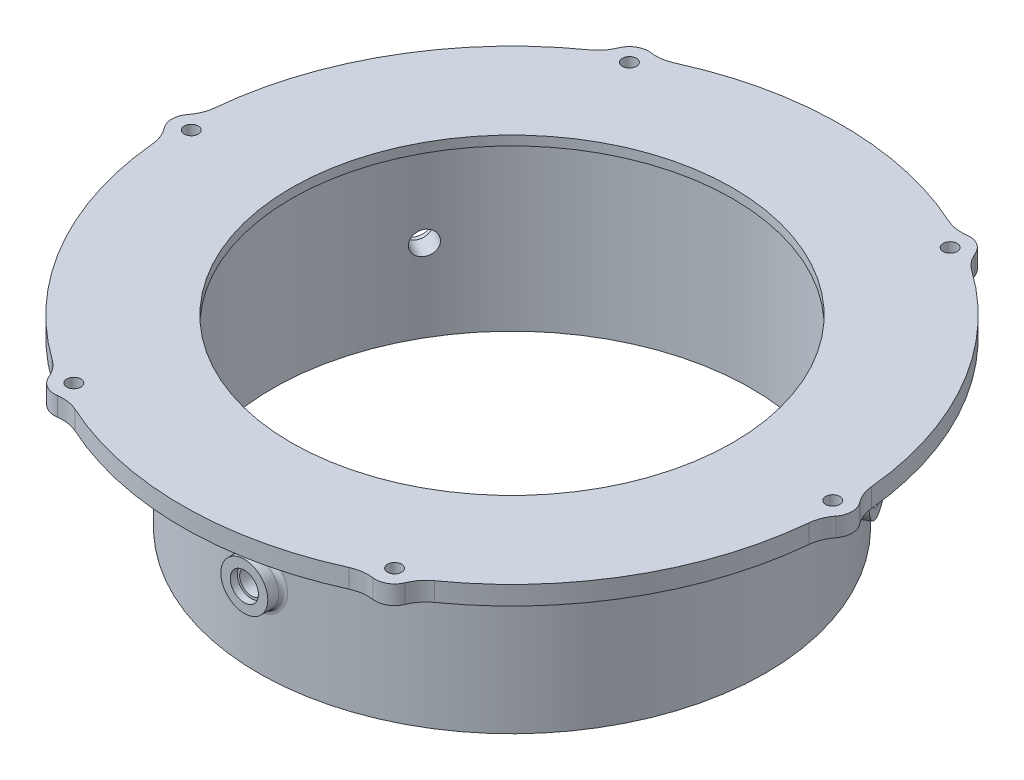
SolidWorks part; units mm, degrees
material "PET"
ref_plane "Front Plane" through (0, 0, 0) normal (0, 0, 1) x (1, 0, 0)
ref_plane "Top Plane" through (0, 0, 0) normal (0, 1, 0) x (1, 0, 0)
ref_plane "Right Plane" through (0, 0, 0) normal (1, 0, 0) x (0, 0, -1)
sketch "Sketch2" plane through (0, 0, 0) normal (0, 0, 1) x (1, 0, 0)
  line L0 (-70.2, -3.2) -> (-47, -3.2)
  line L1 (-47, -3.2) -> (-47, -5.2)
  line L2 (-47, -5.2) -> (-51, -5.2)
  line L3 (-51, -5.2) -> (-51, -42.2)
  line L4 (-51, -42.2) -> (-54, -42.2)
  line L5 (-54, -42.2) -> (-54, -7.2)
  line L6 (-54, -7.2) -> (-70.2, -7.2)
  line L7 (-70.2, -7.2) -> (-70.2, -3.2)
  line L9 (0, 0) -> (0, 30.013) construction
sketch "Sketch3" plane through (0, 0, 0) normal (0, 0, 1) x (1, 0, 0)
  line L8 (-47, -3.2) -> (-70.2, -3.2)
  line L9 (-47, -5.2) -> (-47, -3.2)
  line L10 (-51, -5.2) -> (-47, -5.2)
  line L11 (-51, -42.2) -> (-51, -5.2)
  line L12 (-54, -42.2) -> (-51, -42.2)
  line L13 (-54, -7.2) -> (-54, -42.2)
  line L14 (-70.2, -7.2) -> (-54, -7.2)
  line L15 (-70.2, -3.2) -> (-70.2, -7.2)
  line L16 (-47, -3.2) -> (-70.2, -3.2)
  line L17 (-47, -5.2) -> (-47, -3.2)
  line L18 (-51, -5.2) -> (-47, -5.2)
  line L19 (-51, -42.2) -> (-51, -5.2)
  line L20 (-54, -42.2) -> (-51, -42.2)
  line L21 (-54, -7.2) -> (-54, -42.2)
  line L22 (-70.2, -7.2) -> (-54, -7.2)
  line L23 (-70.2, -3.2) -> (-70.2, -7.2)
  dimension "D1" = 0
revolve "FRA400 100mm" add sketch "Sketch3" angle 360 about L9
sketch "Sketch4" plane through (0, 0, 0) normal (0, 1, 0) x (1, 0, 0)
  circle A0 centre (-68.3, 0) radius 4.1
  circle A1 centre (-68.3, 0) radius 2.1
  point P0 (-68.3, 0)
  point P2 (-70.4, 0)
sketch "Sketch5" plane through (0, 0, 0) normal (0, 1, 0) x (1, 0, 0)
  circle A0 centre (-68.3, 0) radius 4.1 construction
  circle A1 centre (-68.3, 0) radius 4.1
extrude "Boss-Extrude1" add sketch "Sketch5" against normal up to surface (4 mm away) from surface at -3.2 up to face at (54, -7.2, 0) starting at face at (70.2, -3.2, 0)
fillet "Fillet1" radius 8 2 edges at (-70.1034, -5.2, -3.6821) (-70.1034, -5.2, 3.6821)
hole_wizard "CSK for M3 Flat Head Machine Screw1" positions "Sketch8" profile "Sketch9" countersink size "M3" standard "ANSI Metric"
sketch "Sketch8" plane through (0, -7.2, 0) normal (0, -1, 0) x (-1, 0, 0)
  point P0 (68.3, 0)
sketch "Sketch9" plane through (-68.3, -7.2, 0) normal (1, 0, 0) x (0, 0, -1)
  line L0 (0, 0) -> (0, 9.7913)
  line L1 (0, 9.7913) -> (1.5, 8.89)
  line L2 (1.5, 8.89) -> (1.5, 1.6)
  line L3 (1.5, 1.6) -> (3.1, 0)
  line L5 (3.1, 0) -> (0, 0)
  line L6 (-1.5, 1.6) -> (-3.1, 0) construction
  line L10 (0, 9.7913) -> (-1.5, 8.89) construction
  line L11 (0, -6.35) -> (0, 107.95) construction
  dimension "Hole Dia." = 3
  dimension "Hole Depth" = 8.89
  dimension "Near C'Sink Dia." = 6.2
  dimension "Near C'Sink Angle" = 90
  dimension "Drill Angle" = 118
pattern_circular "CirPattern1" count 6 over 360 about axis through (0, 0, 0) along (0, 1, 0) of "Boss-Extrude1", "Fillet1", "CSK for M3 Flat Head Machine Screw1"
ref_plane "Plane1" through (0, 0, 54) normal (0, 0, 1) x (1, 0, 0)
sketch "Sketch14" plane through (0, 0, 54) normal (0, 0, 1) x (1, 0, 0)
  line L0 (0, -7.2) -> (0, -42.2) construction
  line L1 (-54, -42.2) -> (54, -42.2) construction
  line L2 (-29.1602, -7.2) -> (29.1602, -7.2) construction
  circle A0 centre (0, -24.7) radius 5
  point P5 (0, -24.7)
  dimension "D1" = 10
extrude "Boss-Extrude3" add sketch "Sketch14" along normal blind 3 and the other way up to surface
sketch "Sketch15" plane through (0, 0, 54) normal (0, 0, 1) x (1, 0, 0)
  circle A0 centre (0, -24.7) radius 2.5
  dimension "D1" = 5
extrude "Cut-Extrude11" cut sketch "Sketch15" against normal up to surface (6.0613 mm away) from surface at 3 starting at face at (5, -24.7, 57)
sketch "Sketch16" plane through (0, 0, 54) normal (0, 0, 1) x (1, 0, 0)
  circle A0 centre (0, -24.7) radius 3
  dimension "D1" = 6
extrude "Cut-Extrude12" cut sketch "Sketch16" against normal blind 1.5 from surface at 3 starting at face at (2.5, -24.7, 57)
fillet "Fillet2" radius 1 1 edges at (4.8716, -23.574, 53.7798)
pattern_circular "CirPattern3" count 3 over 360 about axis through (0, 0, 0) along (0, 1, 0) of "Boss-Extrude3", "Fillet2", "Cut-Extrude11", "Cut-Extrude12"
equation "\"TopHoles\"= 6"
equation "\"BottomHoles\"=6"
equation "\"D1@CirPattern1\"=\"BottomHoles\""
equation "\"FilterDiameter\" = 110"
equation "\"TelescopeDiameter\"= 102"
equation "\"FilterHeight\"= 8.1"
equation "\"AdapterHoles\"= 3"
